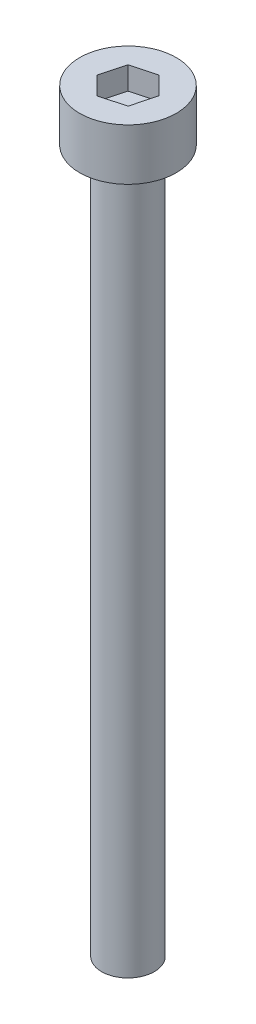
SolidWorks part; units mm, degrees
ref_plane "前视基准面" through (0, 0, 0) normal (0, 0, 1) x (1, 0, 0)
ref_plane "上视基准面" through (0, 0, 0) normal (0, 1, 0) x (1, 0, 0)
ref_plane "右视基准面" through (0, 0, 0) normal (1, 0, 0) x (0, 0, -1)
sketch "草图1" plane through (0, 0, 0) normal (0, 1, 0) x (1, 0, 0)
  circle A0 centre (0, 0) radius 1.5
  dimension "D1" = 3
extrude "凸台-拉伸1" add sketch "草图1" along normal blind 40
sketch "草图2" plane through (0, 40, 0) normal (0, 1, 0) x (1, 0, 0)
  circle A0 centre (0, 0) radius 2.75
  dimension "D1" = 5.5
extrude "凸台-拉伸2" add sketch "草图2" along normal blind 2.93
sketch "草图3" plane through (0, 42.93, 0) normal (0, 1, 0) x (1, 0, 0)
  line L1 (1.024, -1.0172) -> (1.3929, 0.3782)
  line L2 (1.3929, 0.3782) -> (0.3689, 1.3954)
  line L3 (0.3689, 1.3954) -> (-1.024, 1.0172)
  line L4 (-1.024, 1.0172) -> (-1.3929, -0.3782)
  line L5 (-1.3929, -0.3782) -> (-0.3689, -1.3954)
  line L6 (-0.3689, -1.3954) -> (1.024, -1.0172)
  circle A0 centre (0, 0) radius 1.25 construction
  dimension "D1" = 2.5
extrude "切除-拉伸1" cut sketch "草图3" against normal blind 1.3
